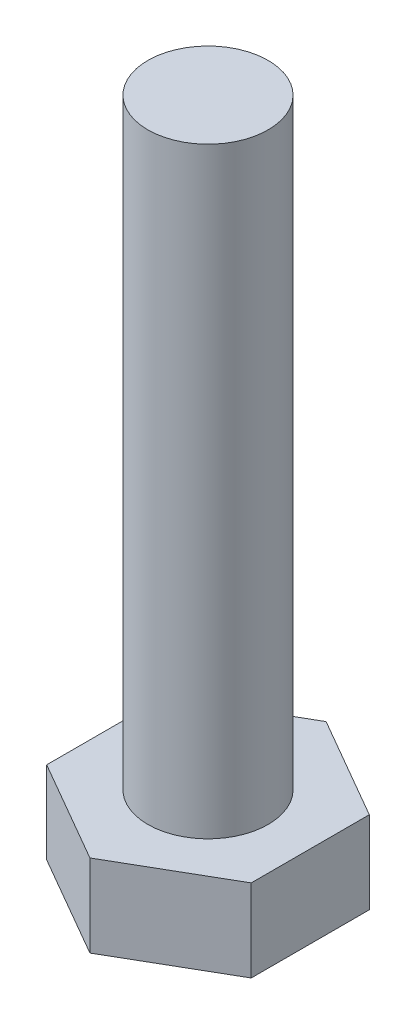
SolidWorks part; units mm, degrees
ref_plane "Спереди" through (0, 0, 0) normal (0, 0, 1) x (1, 0, 0)
ref_plane "Сверху" through (0, 0, 0) normal (0, 1, 0) x (1, 0, 0)
ref_plane "Справа" through (0, 0, 0) normal (1, 0, 0) x (0, 0, -1)
sketch "Эскиз1" plane through (0, 0, 0) normal (0, 1, 0) x (1, 0, 0)
  line L1 (8.5, -4.9075) -> (8.5, 4.9075)
  line L2 (8.5, 4.9075) -> (0, 9.815)
  line L3 (0, 9.815) -> (-8.5, 4.9075)
  line L4 (-8.5, 4.9075) -> (-8.5, -4.9075)
  line L5 (-8.5, -4.9075) -> (0, -9.815)
  line L6 (0, -9.815) -> (8.5, -4.9075)
  circle A0 centre (0, 0) radius 8.5 construction
extrude "Бобышка-Вытянуть1" add sketch "Эскиз1" along normal blind 8
sketch "Эскиз2" plane through (0, 8, 0) normal (0, 1, 0) x (1, 0, 0)
  circle A0 centre (0, 0) radius 5
extrude "Бобышка-Вытянуть2" add sketch "Эскиз2" along normal blind 50
chamfer "Фаска1" distance 2 angle 30 6 edges at (4.25, 0, -7.3612) (8.5, 0, 0) (4.25, 0, 7.3612) (-4.25, 0, 7.3612) (-8.5, 0, 0) (-4.25, 0, -7.3612)
